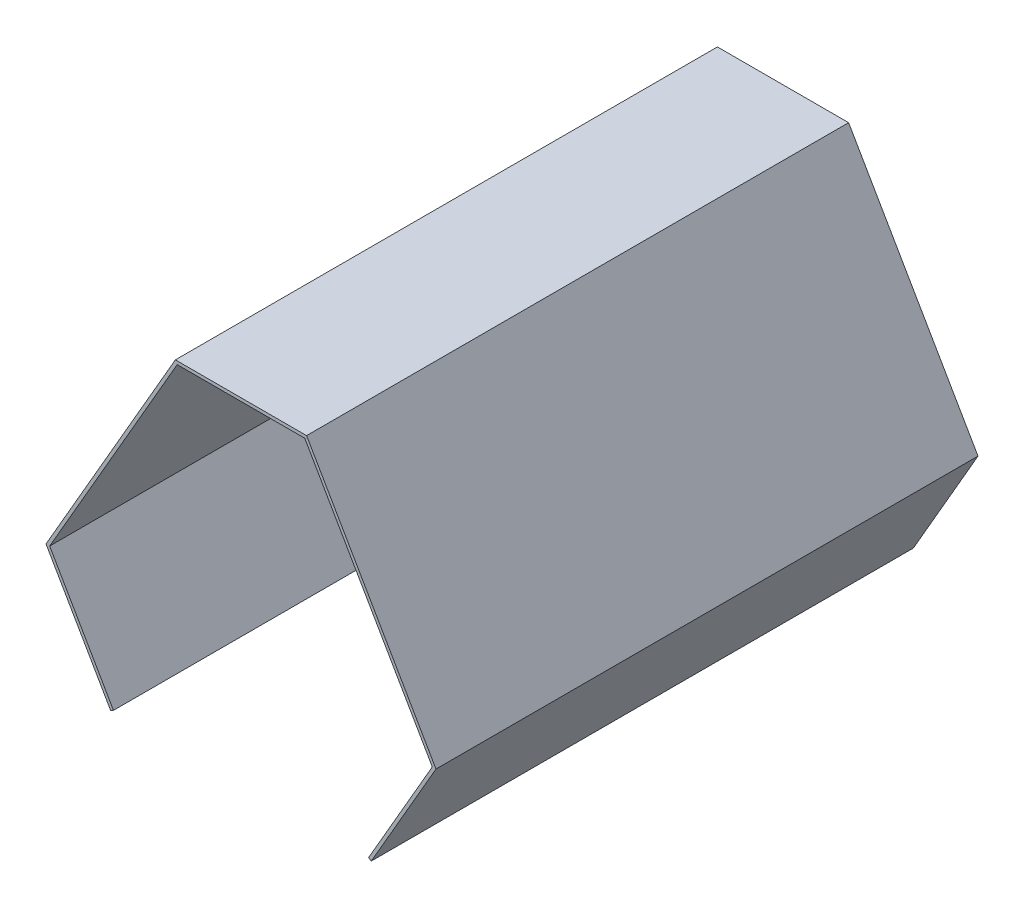
SolidWorks part; units mm, degrees
ref_plane "Front Plane" through (0, 0, 0) normal (0, 0, 1) x (1, 0, 0)
ref_plane "Top Plane" through (0, 0, 0) normal (0, 1, 0) x (1, 0, 0)
ref_plane "Right Plane" through (0, 0, 0) normal (1, 0, 0) x (0, 0, -1)
sketch "Sketch1" plane through (0, 0, 0) normal (0, 0, 1) x (1, 0, 0)
  line L0 (-100, 259.8076) -> (100, 259.8076)
  line L1 (100, 259.8076) -> (300, -86.6025)
  line L2 (300, -86.6025) -> (200, -259.8076)
  line L4 (-200, -259.8076) -> (-300, -86.6025)
  line L5 (-300, -86.6025) -> (-100, 259.8076)
  line L6 (-200, -259.8076) -> (200, -259.8076) construction
  line L7 (-204.3301, -262.3076) -> (-305.7735, -86.6025)
  line L8 (-305.7735, -86.6025) -> (-102.8868, 264.8076)
  line L9 (-102.8868, 264.8076) -> (102.8868, 264.8076)
  line L10 (102.8868, 264.8076) -> (305.7735, -86.6025)
  line L11 (305.7735, -86.6025) -> (204.3301, -262.3076)
  line L12 (-204.3301, -262.3076) -> (-200, -259.8076)
  line L13 (200, -259.8076) -> (204.3301, -262.3076)
  point P3 (0, 259.8076)
  dimension "D1" = 200
  dimension "D2" = 400
  dimension "D3" = 200
  dimension "D4" = 400
  dimension "D5" = 200
  dimension "D6" = 400
  dimension "D7" = 120
  dimension "D8" = 259.8076
  dimension "D9" = 300
  dimension "D10" = 5
extrude "Boss-Extrude1" add sketch "Sketch1" along normal blind 850
